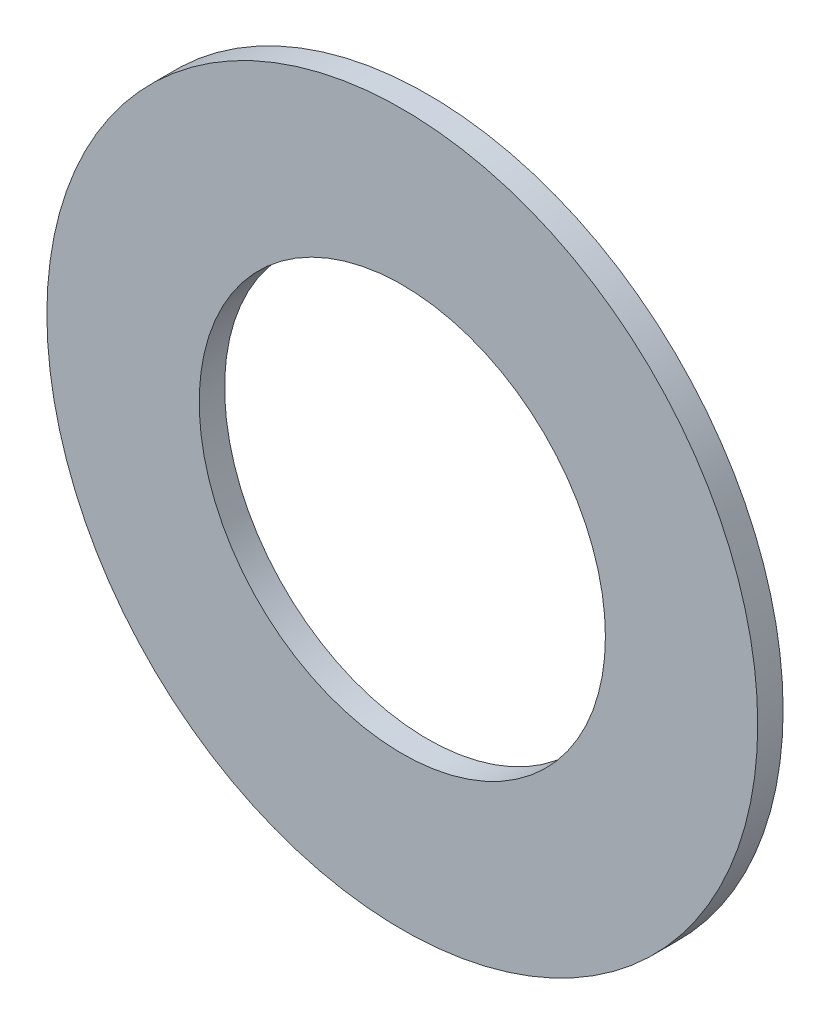
SolidWorks part; units mm, degrees
ref_plane "Front Plane" through (0, 0, 0) normal (0, 0, 1) x (1, 0, 0)
ref_plane "Top Plane" through (0, 0, 0) normal (0, 1, 0) x (1, 0, 0)
ref_plane "Right Plane" through (0, 0, 0) normal (1, 0, 0) x (0, 0, -1)
sketch "Sketch1" plane through (0, 0, 0) normal (0, 0, 1) x (1, 0, 0)
  circle A0 centre (0, 0) radius 7
  circle A1 centre (0, 0) radius 4
  dimension "D1" = 14
  dimension "D2" = 8
extrude "Boss-Extrude1" add sketch "Sketch1" along normal blind 0.5
